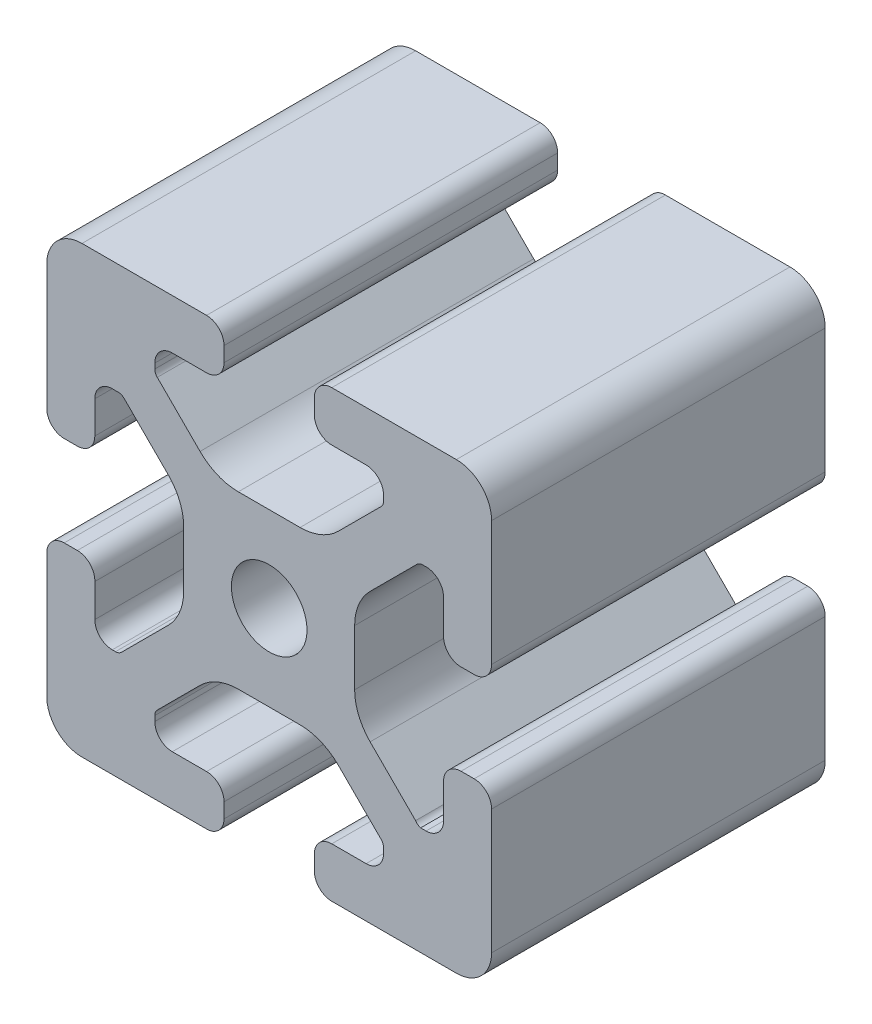
SolidWorks part; units mm, degrees
material "6061 Alloy"
ref_plane "Front Plane" through (0, 0, 0) normal (0, 0, 1) x (1, 0, 0)
ref_plane "Top Plane" through (0, 0, 0) normal (0, 1, 0) x (1, 0, 0)
ref_plane "Right Plane" through (0, 0, 0) normal (1, 0, 0) x (0, 0, -1)
sketch "Sketch1" plane through (0, 0, 0) normal (0, 0, 1) x (1, 0, 0)
  line L0 (0, 19.7407) -> (0, -19.7407) construction
  line L1 (19.0335, 0) -> (-20.7246, 0) construction
  line L2 (-8.715, -15.5246) -> (-5.63, -15.5246)
  line L3 (-10.285, -13.9546) -> (-10.285, -13.4925)
  line L4 (-6.2171, -9.1098) -> (-10.0624, -12.9551)
  line L5 (2.7773, -7.685) -> (-2.7773, -7.685)
  line L6 (10.0624, -12.9551) -> (6.2171, -9.1098)
  line L7 (10.285, -13.9546) -> (10.285, -13.4925)
  line L8 (5.63, -15.5246) -> (8.715, -15.5246)
  line L9 (4.06, -18.43) -> (4.06, -17.0946)
  line L10 (-4.06, -18.43) -> (-4.06, -17.0946)
  line L11 (15.68, -8.7154) -> (15.68, -5.63)
  line L12 (-14.11, -10.2854) -> (-13.8169, -10.2854)
  line L13 (20, -16.83) -> (20, -5.63)
  line L14 (20, 5.63) -> (20, 13.0011)
  line L15 (-16.83, 20) -> (-5.63, 20)
  line L16 (5.63, 20) -> (12.9796, 20)
  line L18 (-8.715, 15.5246) -> (-5.63, 15.5246)
  line L19 (-20, -17.0184) -> (-20, -5.7579)
  line L20 (-20, 5.573) -> (-20, 13.0045)
  line L21 (-15.68, -8.7154) -> (-15.68, -5.7579)
  line L23 (-16.6746, -20) -> (-5.63, -20)
  line L24 (5.63, -20) -> (13, -20)
  line L53 (14.11, -10.2854) -> (13.6201, -10.2854)
  line L54 (13.1637, -9.947) -> (9.0762, -5.8595)
  line L55 (7.685, -2.5008) -> (7.685, 2.5008)
  line L56 (9.0762, 5.8595) -> (13.2795, 10.0628)
  line L57 (13.8169, 10.2854) -> (14.11, 10.2854)
  line L58 (15.68, 8.7154) -> (15.68, 5.63)
  line L59 (17.25, 4.06) -> (18.43, 4.06)
  line L61 (20, 13.0011) -> (20, 16.83)
  line L62 (16.83, 20) -> (12.9796, 20)
  line L64 (4.06, 18.43) -> (4.06, 17.0946)
  line L65 (5.63, 15.5246) -> (8.715, 15.5246)
  line L66 (10.285, 13.9546) -> (10.285, 13.4925)
  line L67 (10.0624, 12.9551) -> (6.2171, 9.1098)
  line L68 (2.7773, 7.685) -> (-2.7773, 7.685)
  line L69 (-6.2171, 9.1098) -> (-10.0624, 12.9551)
  line L70 (-10.285, 13.4925) -> (-10.285, 13.9546)
  line L72 (-4.06, 17.0946) -> (-4.06, 18.43)
  line L75 (-20, 16.83) -> (-20, 13.0045)
  line L77 (-18.43, 4.003) -> (-17.25, 4.003)
  line L78 (-15.68, 5.573) -> (-15.68, 8.4757)
  line L79 (-14.0552, 10.0447) -> (-13.7199, 10.033)
  line L80 (-13.0405, 9.8238) -> (-9.0762, 5.8595)
  line L81 (-7.685, 2.5008) -> (-7.685, -2.5008)
  line L82 (-9.0762, -5.8595) -> (-13.2795, -10.0628)
  line L85 (-17.25, -4.1204) -> (-18.43, -4.1204)
  line L100 (13, -20) -> (16.83, -20)
  line L103 (18.43, -4.06) -> (17.25, -4.06)
  arc A0 (-5.63, -15.5246) -> (-4.06, -17.0946) centre (-5.63, -17.0946) cw
  arc A1 (-8.715, -15.5246) -> (-10.285, -13.9546) centre (-8.715, -13.9546) cw
  arc A2 (-10.285, -13.4925) -> (-10.0624, -12.9551) centre (-9.525, -13.4925) cw
  arc A3 (-6.2171, -9.1098) -> (-2.7773, -7.685) centre (-2.7773, -12.5496) cw
  arc A4 (2.7773, -7.685) -> (6.2171, -9.1098) centre (2.7773, -12.5496) cw
  arc A5 (10.0624, -12.9551) -> (10.285, -13.4925) centre (9.525, -13.4925) cw
  arc A6 (10.285, -13.9546) -> (8.715, -15.5246) centre (8.715, -13.9546) cw
  arc A7 (4.06, -17.0946) -> (5.63, -15.5246) centre (5.63, -17.0946) cw
  arc A8 (5.63, -20) -> (4.06, -18.43) centre (5.63, -18.43) cw
  arc A9 (-4.06, -18.43) -> (-5.63, -20) centre (-5.63, -18.43) cw
  circle A45 centre (0, 0) radius 3.4
  arc A46 (17.25, -4.06) -> (15.68, -5.63) centre (17.25, -5.63) ccw
  arc A47 (14.11, -10.2854) -> (15.68, -8.7154) centre (14.11, -8.7154) ccw
  arc A48 (13.1637, -9.947) -> (13.6201, -10.2854) centre (13.8117, -9.55) ccw
  arc A49 (7.685, -2.5008) -> (9.0762, -5.8595) centre (12.435, -2.5008) ccw
  arc A50 (9.0762, 5.8595) -> (7.685, 2.5008) centre (12.435, 2.5008) ccw
  arc A51 (13.8169, 10.2854) -> (13.2795, 10.0628) centre (13.8169, 9.5254) ccw
  arc A52 (15.68, 8.7154) -> (14.11, 10.2854) centre (14.11, 8.7154) ccw
  arc A53 (15.68, 5.63) -> (17.25, 4.06) centre (17.25, 5.63) ccw
  arc A54 (18.43, 4.06) -> (20, 5.63) centre (18.43, 5.63) ccw
  arc A55 (20, 16.83) -> (16.83, 20) centre (16.83, 16.83) ccw
  arc A56 (5.63, 20) -> (4.06, 18.43) centre (5.63, 18.43) ccw
  arc A57 (4.06, 17.0946) -> (5.63, 15.5246) centre (5.63, 17.0946) ccw
  arc A58 (10.285, 13.9546) -> (8.715, 15.5246) centre (8.715, 13.9546) ccw
  arc A59 (10.0624, 12.9551) -> (10.285, 13.4925) centre (9.525, 13.4925) ccw
  arc A60 (2.7773, 7.685) -> (6.2171, 9.1098) centre (2.7773, 12.5496) ccw
  arc A61 (-6.2171, 9.1098) -> (-2.7773, 7.685) centre (-2.7773, 12.5496) ccw
  arc A62 (-10.285, 13.4925) -> (-10.0624, 12.9551) centre (-9.525, 13.4925) ccw
  arc A63 (-8.715, 15.5246) -> (-10.285, 13.9546) centre (-8.715, 13.9546) ccw
  arc A64 (-5.63, 15.5246) -> (-4.06, 17.0946) centre (-5.63, 17.0946) ccw
  arc A65 (-4.06, 18.43) -> (-5.63, 20) centre (-5.63, 18.43) ccw
  arc A66 (-16.83, 20) -> (-20, 16.83) centre (-16.83, 16.83) ccw
  arc A67 (-20, 5.573) -> (-18.43, 4.003) centre (-18.43, 5.573) ccw
  arc A68 (-17.25, 4.003) -> (-15.68, 5.573) centre (-17.25, 5.573) ccw
  arc A69 (-14.0552, 10.0447) -> (-15.68, 8.4757) centre (-14.11, 8.4757) ccw
  arc A70 (-13.0405, 9.8238) -> (-13.7199, 10.033) centre (-13.5779, 9.2864) ccw
  arc A71 (-7.685, 2.5008) -> (-9.0762, 5.8595) centre (-12.435, 2.5008) ccw
  arc A72 (-9.0762, -5.8595) -> (-7.685, -2.5008) centre (-12.435, -2.5008) ccw
  arc A73 (-13.8169, -10.2854) -> (-13.2795, -10.0628) centre (-13.8169, -9.5254) ccw
  arc A74 (-15.68, -8.7154) -> (-14.11, -10.2854) centre (-14.11, -8.7154) ccw
  arc A75 (-15.68, -5.7579) -> (-17.25, -4.1204) centre (-17.2485, -5.6904) ccw
  arc A76 (-18.43, -4.1204) -> (-20, -5.7579) centre (-18.4315, -5.6904) ccw
  arc A77 (-20, -17.0184) -> (-16.6746, -20) centre (-16.8354, -16.8341) ccw
  arc A88 (16.83, -20) -> (20, -16.83) centre (16.83, -16.83) ccw
  arc A89 (20, -5.63) -> (18.43, -4.06) centre (18.43, -5.63) ccw
  dimension "D2" = 6.8
  dimension "D7" = 20.57
  dimension "D1" = 40
  dimension "D3" = 4.32
  dimension "D4" = 15.37
  dimension "D5" = 20
  dimension "D6" = 4.32
  dimension "D9" = 15.37
extrude "Extrude1" add sketch "Sketch1" against normal blind 30
